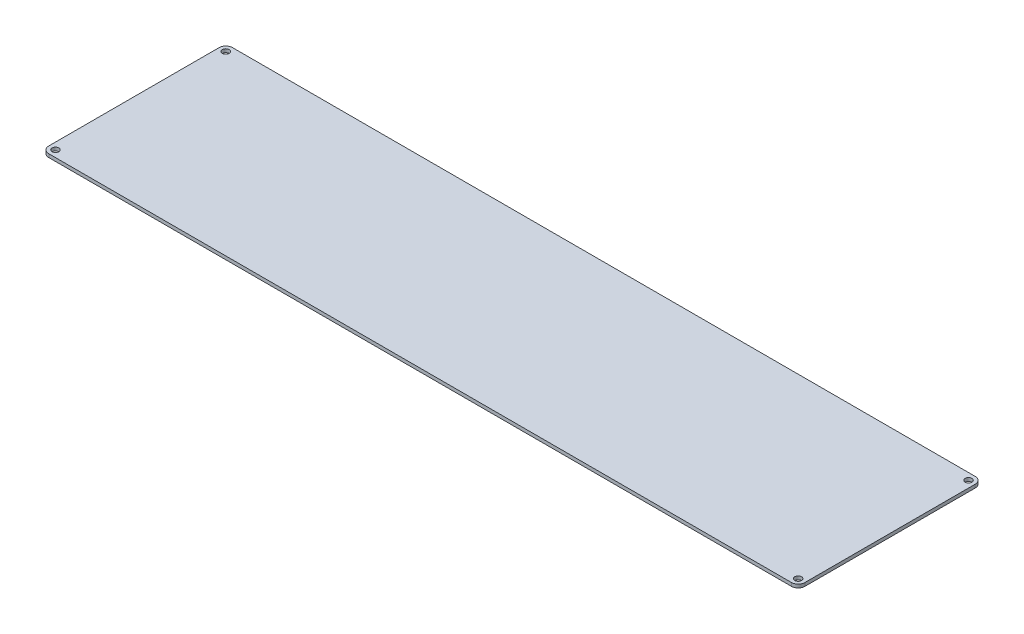
SolidWorks part; units mm, degrees
material "Delrin 2700 NC010, Low Viscosity Acetal Copolymer (SS)"
ref_plane "Front" through (0, 0, 0) normal (0, 0, 1) x (1, 0, 0)
ref_plane "Top" through (0, 0, 0) normal (0, 1, 0) x (1, 0, 0)
ref_plane "Right" through (0, 0, 0) normal (1, 0, 0) x (0, 0, -1)
sketch "Sketch1" plane through (0, 0, 0) normal (0, 1, 0) x (1, 0, 0)
  line L0 (13.7815, 113.4471) -> (20.1315, 113.4471) construction
  line L5 (-25.0185, 167.2471) -> (13.7815, 167.2471) construction
  line L6 (-25.0185, 167.2471) -> (-25.0185, 113.4471) construction
  line L7 (-25.0185, 113.4471) -> (13.7815, 113.4471) construction
  line L8 (13.7815, 167.2471) -> (13.7815, 113.4471) construction
  line L9 (-131.3685, 167.2471) -> (-31.3685, 167.2471) construction
  line L10 (-131.3685, 167.2471) -> (-131.3685, 77.2471) construction
  line L11 (-131.3685, 77.2471) -> (-31.3685, 77.2471) construction
  line L12 (-31.3685, 167.2471) -> (-31.3685, 77.2471) construction
  line L13 (20.1315, 167.2471) -> (58.9315, 167.2471) construction
  line L14 (20.1315, 167.2471) -> (20.1315, 113.4471) construction
  line L15 (20.1315, 113.4471) -> (58.9315, 113.4471) construction
  line L16 (58.9315, 167.2471) -> (58.9315, 113.4471) construction
  line L17 (65.2815, 167.2471) -> (104.0815, 167.2471) construction
  line L18 (65.2815, 167.2471) -> (65.2815, 113.4471) construction
  line L19 (65.2815, 113.4471) -> (104.0815, 113.4471) construction
  line L20 (104.0815, 167.2471) -> (104.0815, 113.4471) construction
  line L21 (58.9315, 113.4471) -> (65.2815, 113.4471) construction
  line L22 (-373.4896, 192.6471) -> (327.6015, 192.6471) construction
  line L27 (-379.8396, 198.9971) -> (333.9515, 198.9971)
  line L28 (-379.8396, 198.9971) -> (-379.8396, 25.5151)
  line L29 (-379.8396, 25.5151) -> (333.9515, 25.5151)
  line L30 (333.9515, 198.9971) -> (333.9515, 25.5151)
  line L31 (327.6015, 192.6471) -> (327.6015, 31.8651) construction
  line L32 (-373.4896, 31.8651) -> (327.6015, 31.8651) construction
  line L33 (-373.4896, 192.6471) -> (-373.4896, 31.8651) construction
  line L34 (-25.0185, 167.2471) -> (-31.3685, 167.2471) construction
  line L35 (104.0815, 167.2471) -> (110.4315, 167.2471) construction
  line L36 (110.4315, 167.2471) -> (308.5515, 167.2471) construction
  line L37 (110.4315, 167.2471) -> (110.4315, 57.2651) construction
  line L38 (110.4315, 57.2651) -> (308.5515, 57.2651) construction
  line L39 (308.5515, 167.2471) -> (308.5515, 57.2651) construction
  line L41 (-367.1396, 182.1061) -> (-367.1396, 42.4061) construction
  circle A0 centre (-373.4896, 192.6471) radius 3.175
  circle A1 centre (-373.4896, 31.8651) radius 3.175
  circle A2 centre (327.6015, 31.8651) radius 3.175
  circle A3 centre (327.6015, 192.6471) radius 3.175
  dimension "D14" = 6.35
  dimension "D2" = 12.7
  dimension "D3" = 38.8
  dimension "D4" = 100
  dimension "D5" = 90
  dimension "D6" = 53.8
  dimension "D7" = 25.4
  dimension "D8" = 25.4
  dimension "D9" = 198.12
  dimension "D10" = 6.35
  dimension "D11" = 19.05
  dimension "D12" = 109.982
  dimension "D13" = 6.35
extrude "Boss-Extrude1" add sketch "Sketch1" against normal blind 3.175 contours L30 L27 L28 L29 A3 A2 A1 A0
fillet "Fillet1" radius 6.35 4 edges at (-379.8396, -1.5875, -198.9971) (-379.8396, -1.5875, -25.5151) (333.9515, -1.5875, -25.5151) (333.9515, -1.5875, -198.9971)
